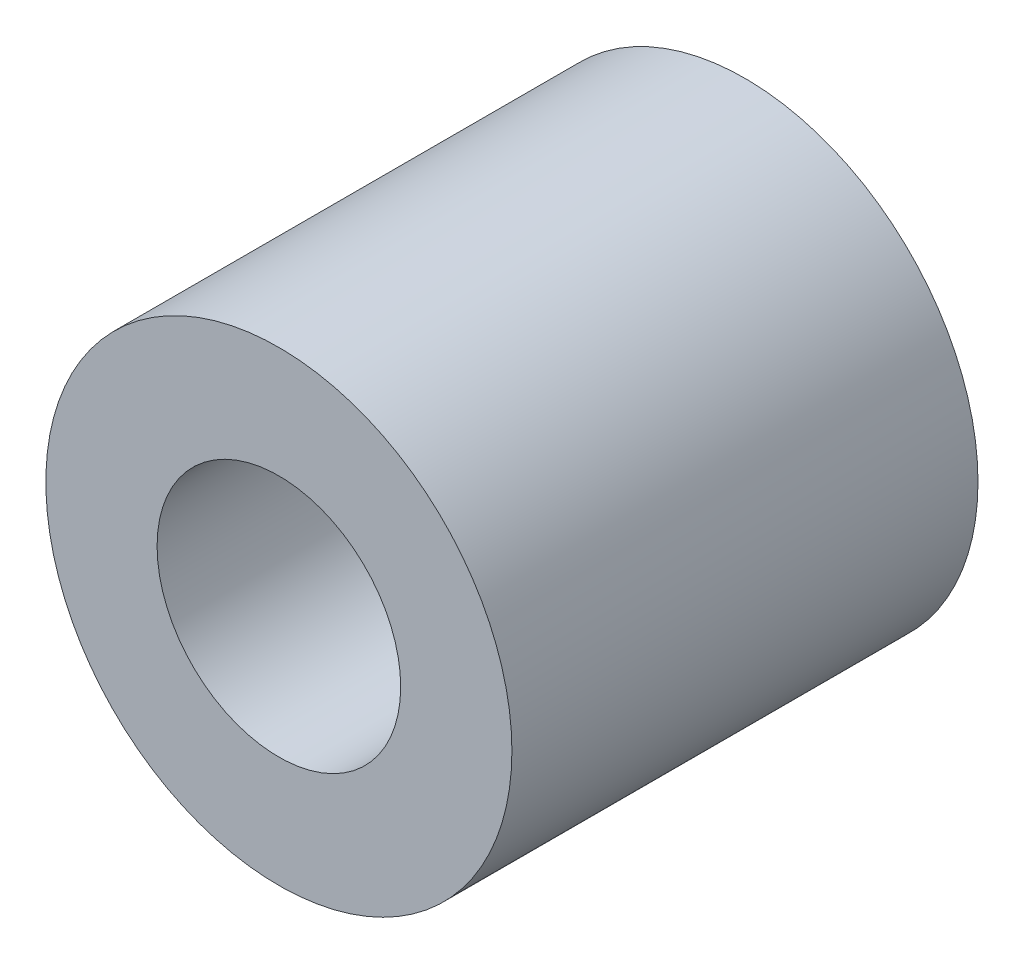
SolidWorks part; units mm, degrees
material "6061-T6 (SS)"
ref_plane "Front Plane" through (0, 0, 0) normal (0, 0, 1) x (1, 0, 0)
ref_plane "Top Plane" through (0, 0, 0) normal (0, 1, 0) x (1, 0, 0)
ref_plane "Right Plane" through (0, 0, 0) normal (1, 0, 0) x (0, 0, -1)
sketch "Sketch1" plane through (0, 0, 0) normal (0, 0, 1) x (1, 0, 0)
  circle A0 centre (0, 0) radius 4.7625
  circle A1 centre (0, 0) radius 2.4892
  dimension "D1" = 9.525
  dimension "D2" = 4.9784
extrude "Boss-Extrude1" add sketch "Sketch1" along normal mid plane 9.525
